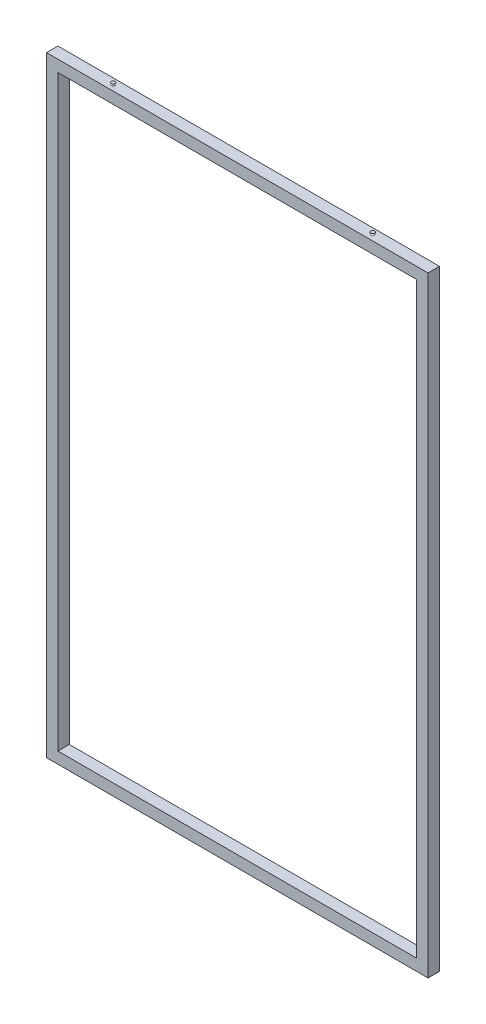
SolidWorks part; units mm, degrees
ref_plane "Front Plane" through (0, 0, 0) normal (0, 0, 1) x (1, 0, 0)
ref_plane "Top Plane" through (0, 0, 0) normal (0, 1, 0) x (1, 0, 0)
ref_plane "Right Plane" through (0, 0, 0) normal (1, 0, 0) x (0, 0, -1)
sketch "Sketch1" plane through (0, 0, 0) normal (0, 0, 1) x (1, 0, 0)
  line L0 (-470, 770) -> (470, 770)
  line L1 (-500, 800) -> (500, 800)
  line L2 (-500, 800) -> (-500, -800)
  line L3 (-500, -800) -> (500, -800)
  line L4 (500, 800) -> (500, -800)
  line L5 (-500, 800) -> (500, -800) construction
  line L6 (-500, -800) -> (500, 800) construction
  line L7 (470, 770) -> (470, -770)
  line L8 (-470, -770) -> (470, -770)
  line L9 (-470, 770) -> (-470, -770)
  point P0 (0, 0)
  dimension "D1" = 1600
  dimension "D2" = 1000
  dimension "D3" = 30
extrude "Boss-Extrude1" add sketch "Sketch1" along normal mid plane 30
sketch "Sketch2" plane through (0, 0, 0) normal (1, 0, 0) x (0, 0, -1)
  line L3 (-15, 800) -> (15, 800) construction
  line L4 (-15, 770) -> (15, 770) construction
  line L5 (-15, 800) -> (15, 800) construction
  line L6 (-15, 770) -> (15, 770) construction
  line L7 (-15, 800) -> (-15, 770) construction
  line L8 (15, 800) -> (15, 770) construction
  line L10 (13, 798) -> (13, 772)
  line L11 (-13, 772) -> (13, 772)
  line L12 (-13, 798) -> (-13, 772)
  line L13 (-13, 798) -> (13, 798)
  dimension "D1" = 2
sketch "Sketch4" plane through (0, 0, 0) normal (0, 0, 1) x (1, 0, 0)
  line L0 (-485, 785) -> (-485, -785)
  line L1 (-485, -785) -> (485, -785)
  line L2 (485, -785) -> (485, 785)
  line L3 (485, 785) -> (-485, 785)
  line L4 (500, -800) -> (500, 800)
  line L5 (500, 800) -> (-500, 800)
  line L6 (-500, 800) -> (-500, -800)
  line L7 (-500, -800) -> (500, -800)
  line L8 (500, -800) -> (500, 800)
  line L9 (500, 800) -> (-500, 800)
  line L10 (-500, 800) -> (-500, -800)
  line L11 (-500, -800) -> (500, -800)
  dimension "D1" = 0
  dimension "D2" = 15
sweep "Cut-Sweep1" cut profiles "Sketch2" path "Sketch4"
sketch "Sketch5" plane through (0, 800, 0) normal (0, 1, 0) x (1, 0, 0)
  line L0 (0, 18.3123) -> (0, -18.3123) construction
  line L6 (500, 15) -> (-500, 15)
  line L7 (-500, 15) -> (-500, -15)
  line L8 (-500, -15) -> (500, -15)
  line L9 (500, -15) -> (500, 15)
  line L10 (500, 15) -> (-500, 15)
  line L11 (-500, 15) -> (-500, -15)
  line L12 (-500, -15) -> (500, -15)
  line L13 (500, -15) -> (500, 15)
  circle A0 centre (-340, 0) radius 15 construction
  circle A1 centre (-340, 0) radius 7
  point P4 (0, 0)
  dimension "D1" = 340
  dimension "D2" = 0
  dimension "D3" = 8
ref_plane "Plane1" through (0, 806.8, 0) normal (0, 1, 0) x (1, 0, 0)
sketch "Sketch6" plane through (0, 806.8, 0) normal (0, 1, 0) x (1, 0, 0)
  circle A2 centre (-340, 0) radius 7 construction
  circle A3 centre (-340, 0) radius 7
sketch "Sketch7" plane through (0, 0, 0) normal (0, 0, 1) x (1, 0, 0)
  line L5 (-340, 800) -> (-340, 805)
  line L6 (-345, 805) -> (-340, 805)
  line L7 (-345, 800) -> (-340, 800)
  line L8 (-340, 795.1043) -> (-340, 811.1427) construction
  arc A0 (-345, 800) -> (-345, 805) centre (-345, 802.5) ccw
  point P12 (-340, 802.5)
  dimension "D1" = 2.5
  dimension "D2" = 5
revolve "Revolve1" add sketch "Sketch7" angle 360 about L8
mirror "Mirror1" about plane through (0, 0, 0) normal (1, 0, 0) of "Revolve1"
sketch "Sketch8" plane through (0, 805, 0) normal (0, 1, 0) x (1, 0, 0)
  circle A1 centre (340, 0) radius 5
  circle A2 centre (340, 0) radius 5
  point P0 (335, 0)
  point P1 (0, 0)
  dimension "D1" = 0
